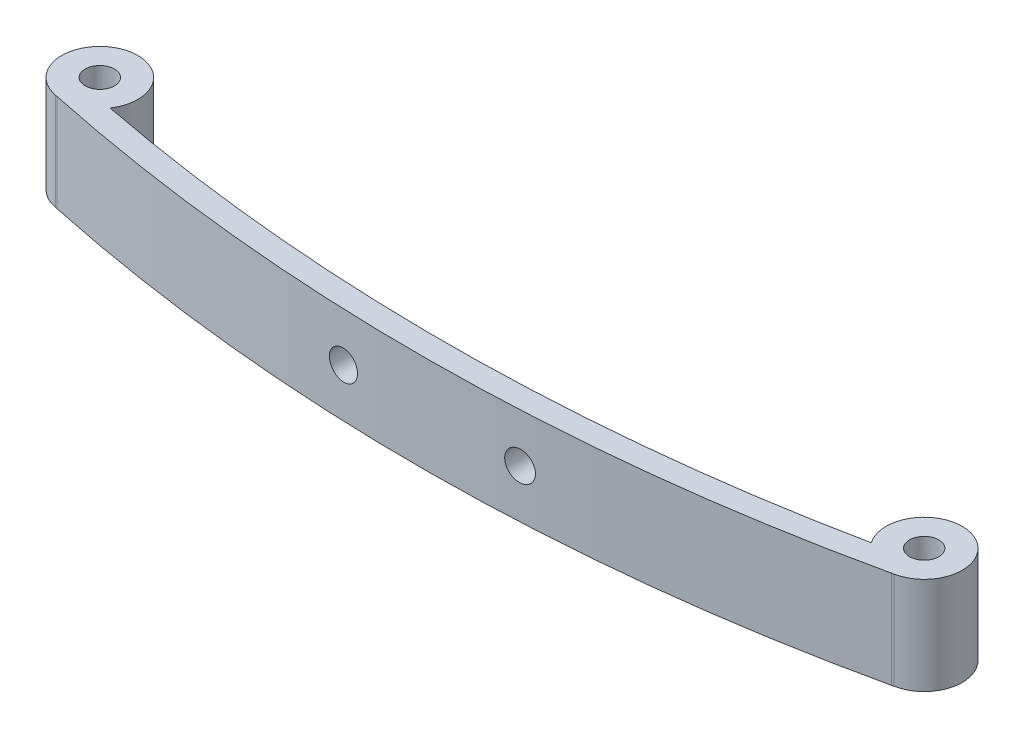
SolidWorks part; units mm, degrees
ref_plane "Front Plane" through (0, 0, 0) normal (0, 0, 1) x (1, 0, 0)
ref_plane "Top Plane" through (0, 0, 0) normal (0, 1, 0) x (1, 0, 0)
ref_plane "Right Plane" through (0, 0, 0) normal (1, 0, 0) x (0, 0, -1)
sketch "Sketch1" plane through (0, 0, 0) normal (0, 1, 0) x (1, 0, 0)
  line L0 (-35, 4.1426) -> (35, 4.5206) construction
  line L1 (35.4342, 1.2875) -> (35.6227, 1.3308)
  line L2 (-35.4132, 0.908) -> (-35.5757, 0.944)
  line L3 (-32.5, 11.9983) -> (-32.5, -12.2817) construction
  line L4 (32.5, 20.0549) -> (32.5, -12.2817) construction
  circle A0 centre (-35, 4.1426) radius 1.25
  circle A1 centre (35, 4.5206) radius 1.25
  arc A2 (-32.3092, 2.3199) -> (-35.5757, 0.944) centre (-35, 4.1426) ccw
  arc A3 (35.6227, 1.3308) -> (32.3291, 2.6689) centre (35, 4.5206) ccw
  arc A4 (-32.3092, 2.3199) -> (32.3291, 2.6689) centre (-0.865, 164.5106) ccw
  arc A5 (-35.4132, 0.908) -> (35.4342, 1.2875) centre (-0.865, 164.5106) ccw
  arc A7 (-35, 2.8648) -> (35, 3.2398) centre (-0.865, 164.5106) ccw construction
  circle A8 centre (-35, 4.1426) radius 3.25 construction
  circle A9 centre (35, 4.5206) radius 3.25 construction
  point P7 (38.108, 5.4708)
  point P18 (-31.892, 5.0928)
  dimension "D1" = 2.5
  dimension "D2" = 2.5
  dimension "D3" = 70
  dimension "D4" = 35
  dimension "D6" = 65
  dimension "D8" = 32.5
  dimension "D9" = 70.001
  dimension "D5" = 2
  dimension "D7" = 2
extrude "Boss-Extrude1" add sketch "Sketch1" along normal blind 8.3
sketch "Sketch2" plane through (0, 0, 0) normal (0, 0, 1) x (1, 0, 0)
  line L0 (0.0105, 8.3) -> (0, 0) construction
  line L1 (35.4342, 8.3) -> (-35.4132, 8.3) construction
  line L2 (35.6227, 4.15) -> (-35.5757, 4.15) construction
  line L5 (35.6227, 8.3) -> (35.6227, 0) construction
  line L6 (-35.5757, 8.3) -> (-35.5757, 0) construction
  circle A0 centre (7.5052, 4.15) radius 1.25
  circle A1 centre (-7.4948, 4.15) radius 1.25
  point P15 (0.0052, 4.15)
  dimension "D2" = 2.5
  dimension "D3" = 2.5
  dimension "D1" = 15
  dimension "D4" = 7.5
extrude "Cut-Extrude1" cut sketch "Sketch2" against normal through all both and the other way through all
